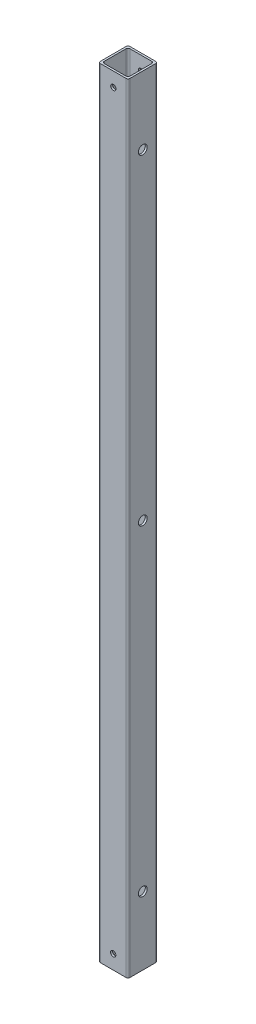
SolidWorks part; units mm, degrees
ref_plane "Front Plane" through (0, 0, 0) normal (0, 0, 1) x (1, 0, 0)
ref_plane "Top Plane" through (0, 0, 0) normal (0, 1, 0) x (1, 0, 0)
ref_plane "Right Plane" through (0, 0, 0) normal (1, 0, 0) x (0, 0, -1)
sketch "Sketch1" plane through (0, 0, 0) normal (0, 1, 0) x (1, 0, 0)
  line L0 (8.382, -8.382) -> (8.382, 8.382)
  line L1 (-9.652, -9.652) -> (9.652, -9.652)
  line L2 (-9.652, -9.652) -> (-9.652, 9.652)
  line L3 (-9.652, 9.652) -> (9.652, 9.652)
  line L4 (9.652, -9.652) -> (9.652, 9.652)
  line L5 (-9.652, -9.652) -> (9.652, 9.652) construction
  line L6 (-9.652, 9.652) -> (9.652, -9.652) construction
  line L7 (-8.382, 8.382) -> (8.382, 8.382)
  line L8 (-8.382, -8.382) -> (-8.382, 8.382)
  line L9 (-8.382, -8.382) -> (8.382, -8.382)
  point P0 (0, 0)
  dimension "D1" = 19.304
  dimension "D2" = 1.27
extrude "Boss-Extrude1" add sketch "Sketch1" along normal blind 508
fillet "Fillet1" radius 1.27 8 edges at (-9.652, 254, 9.652) (-9.652, 254, -9.652) (9.652, 254, -9.652) (9.652, 254, 9.652) (-8.382, 254, -8.382) (8.382, 254, 8.382) (8.382, 254, -8.382) (-8.382, 254, 8.382)
hole_wizard "#1 (0.228) Diameter Hole2" positions "Sketch4" profile "Sketch5" hole size "#1" standard "ANSI Inch" end condition through all
sketch "Sketch4" plane through (-9.652, 0, 0) normal (-1, 0, 0) x (0, 0, 1)
  line L0 (0, 0) -> (0, 508) construction
  line L1 (-8.382, 0) -> (8.382, 0) construction
  line L2 (-8.382, 508) -> (8.382, 508) construction
  point P8 (0, 44.45)
  point P34 (0, 254)
  point P35 (0, 463.55)
  dimension "D1" = 44.45
  dimension "D2" = 3
sketch "Sketch5" plane through (-9.652, 463.55, 0) normal (0, 1, 0) x (0, 0, 1)
  line L0 (0, 0) -> (0, 19.304)
  line L1 (0, 19.304) -> (2.8956, 19.304)
  line L2 (2.8956, 19.304) -> (2.8956, 0)
  line L5 (2.8956, 0) -> (0, 0)
  line L11 (0, -6.35) -> (0, 107.95) construction
  dimension "Thru Hole Dia." = 5.7912
  dimension "Thru Hole Depth" = 19.304
hole_wizard "#8-32 Tapped Hole1" positions "Sketch6" profile "Sketch8" tap size "#8-32" standard "ANSI Inch" end condition through all
sketch "Sketch6" plane through (0, 0, 9.652) normal (0, 0, 1) x (1, 0, 0)
  line L1 (-8.382, 0) -> (8.382, 0) construction
  line L2 (-8.382, 508) -> (8.382, 508) construction
  point P5 (0, 9.271)
  point P15 (0.1031, 498.729)
  dimension "D1" = 9.271
  dimension "D2" = 9.271
sketch "Sketch8" plane through (0, 9.271, 9.652) normal (1, 0, 0) x (0, -1, 0)
  line L0 (0, 0) -> (0, 19.304)
  line L1 (0, 19.304) -> (1.7272, 19.304)
  line L2 (1.7272, 19.304) -> (1.7272, 0)
  line L5 (1.7272, 0) -> (0, 0)
  line L11 (0, -6.35) -> (0, 107.95) construction
  dimension "Thru Tap Drill Dia." = 3.4544
  dimension "Thru Tap Drill Depth" = 19.304
cosmetic thread "Hole Thread1" parameters "D2"=4.1656
cosmetic thread "Hole Thread2" parameters "D2"=4.1656
ref_plane "Plane1" through (-8.382, 508, 9.652) normal (1, 0, 0) x (0, 0, -1)
